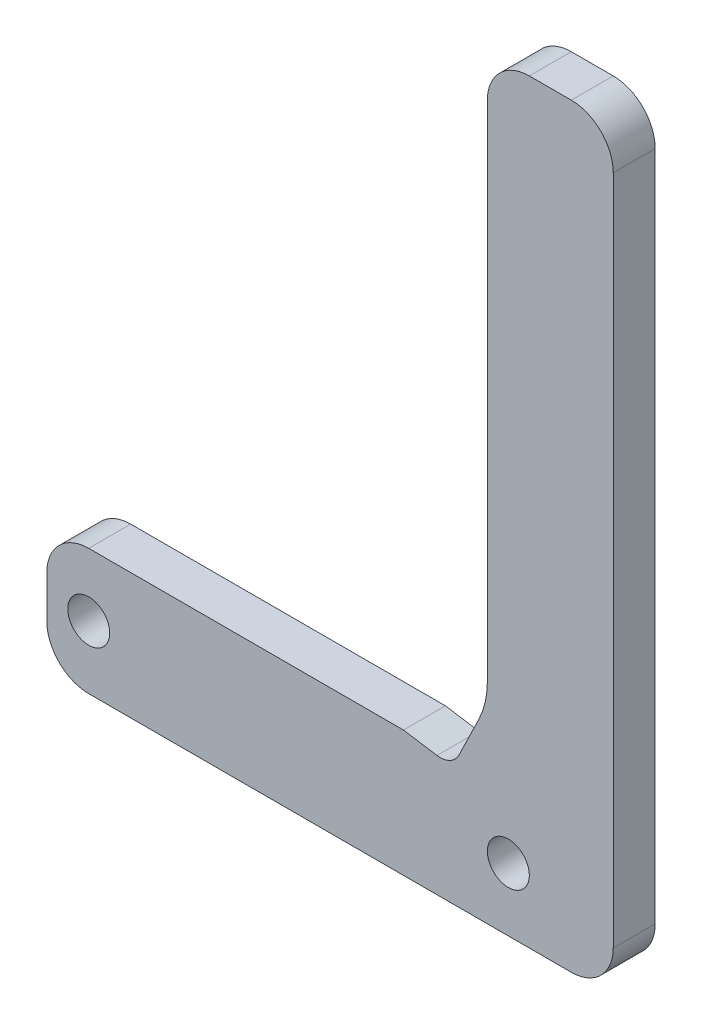
SolidWorks part; units mm, degrees
ref_plane "Front Plane" through (0, 0, 0) normal (0, 0, 1) x (1, 0, 0)
ref_plane "Top Plane" through (0, 0, 0) normal (0, 1, 0) x (1, 0, 0)
ref_plane "Right Plane" through (0, 0, 0) normal (1, 0, 0) x (0, 0, -1)
sketch "Sketch1" plane through (0, 0, 0) normal (0, 0, 1) x (1, 0, 0)
  line L0 (0, 19.05) -> (0, 0)
  line L1 (0, 0) -> (85.725, 0)
  line L2 (85.725, 0) -> (85.725, 114.3)
  line L3 (85.725, 114.3) -> (66.675, 114.3)
  line L4 (66.675, 114.3) -> (66.675, 19.05)
  line L5 (66.675, 19.05) -> (0, 19.05)
  line L6 (0, 9.525) -> (85.725, 9.525) construction
  circle A0 centre (69.85, 9.525) radius 3.175
  circle A1 centre (6.35, 9.525) radius 3.175
  dimension "D2" = 6.35
  dimension "D3" = 6.35
  dimension "D1" = 114.3
  dimension "D4" = 19.05
  dimension "D5" = 3.175
  dimension "D6" = 19.05
  dimension "D7" = 63.5
  dimension "D8" = 6.35
extrude "Boss-Extrude1" add sketch "Sketch1" along normal blind 6.35
fillet "Fillet1" radius 6.35 5 edges at (66.675, 114.3, 3.175) (85.725, 114.3, 3.175) (85.725, 0, 3.175) (0, 0, 3.175) (0, 19.05, 3.175)
fillet "Fillet2" radius 12.7 1 edges at (66.675, 19.05, 3.175)
sketch "Sketch2" plane through (0, 0, 6.35) normal (0, 0, 1) x (1, 0, 0)
  line L1 (59.055, 18.2562) -> (53.975, 19.05)
  line L2 (65.4071, 26.2184) -> (62.4032, 20.0103)
  line L3 (53.975, 19.05) -> (65.4071, 26.2184)
  circle A2 centre (59.5451, 21.3932) radius 3.175
  arc A4 (53.975, 19.05) -> (66.675, 31.75) centre (53.975, 31.75) ccw construction
  arc M9 (66.675, 31.75) -> (53.975, 19.05) centre (53.975, 31.75) cw
  dimension "D1" = 6.35
  dimension "D2" = 0.7937
  dimension "D3" = 5.08
extrude "Cut-Extrude1" cut sketch "Sketch2" against normal through all contours A2 L1 M9 | A2 M9 | A2 L2 M9
